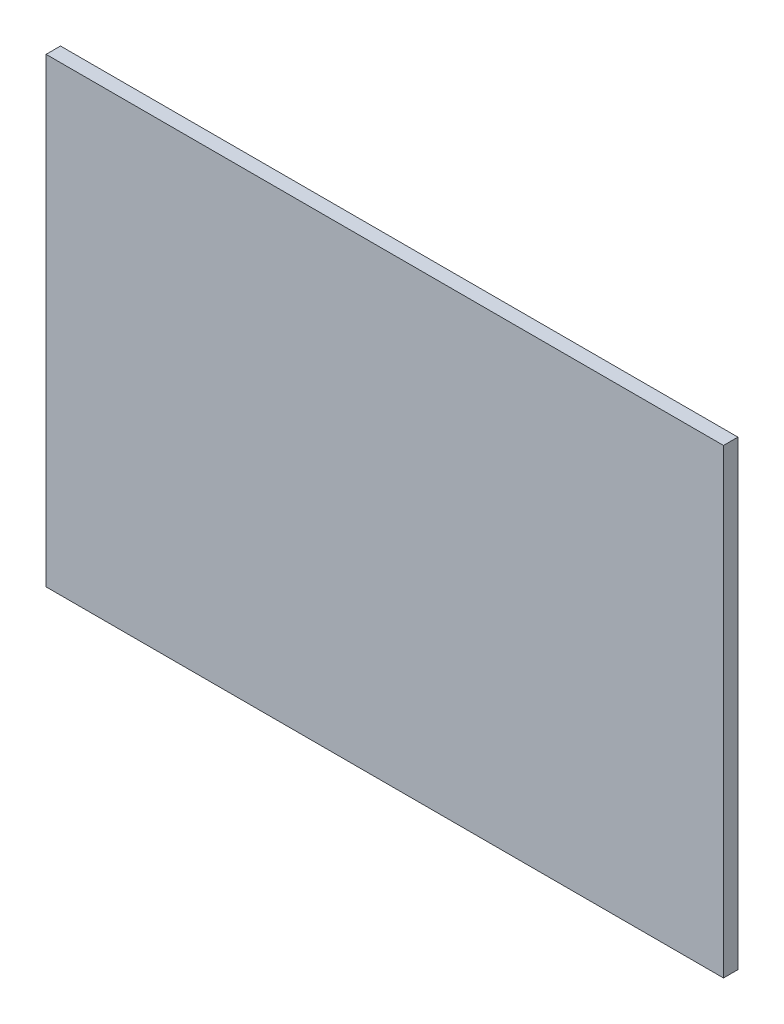
SolidWorks part; units mm, degrees
material "6061-T6 (SS)"
ref_plane "Front Plane" through (0, 0, 0) normal (0, 0, 1) x (1, 0, 0)
ref_plane "Top Plane" through (0, 0, 0) normal (0, 1, 0) x (1, 0, 0)
ref_plane "Right Plane" through (0, 0, 0) normal (1, 0, 0) x (0, 0, -1)
sketch "Sketch1" plane through (0, 0, 0) normal (0, 0, 1) x (1, 0, 0)
  line L1 (-74.6125, 50.8) -> (74.6125, 50.8)
  line L2 (-74.6125, 50.8) -> (-74.6125, -50.8)
  line L3 (-74.6125, -50.8) -> (74.6125, -50.8)
  line L4 (74.6125, 50.8) -> (74.6125, -50.8)
  line L5 (-74.6125, 50.8) -> (74.6125, -50.8) construction
  line L6 (-74.6125, -50.8) -> (74.6125, 50.8) construction
  point P0 (0, 0)
  dimension "D1" = 149.225
  dimension "D2" = 101.6
extrude "Boss-Extrude1" add sketch "Sketch1" along normal blind 3.175
